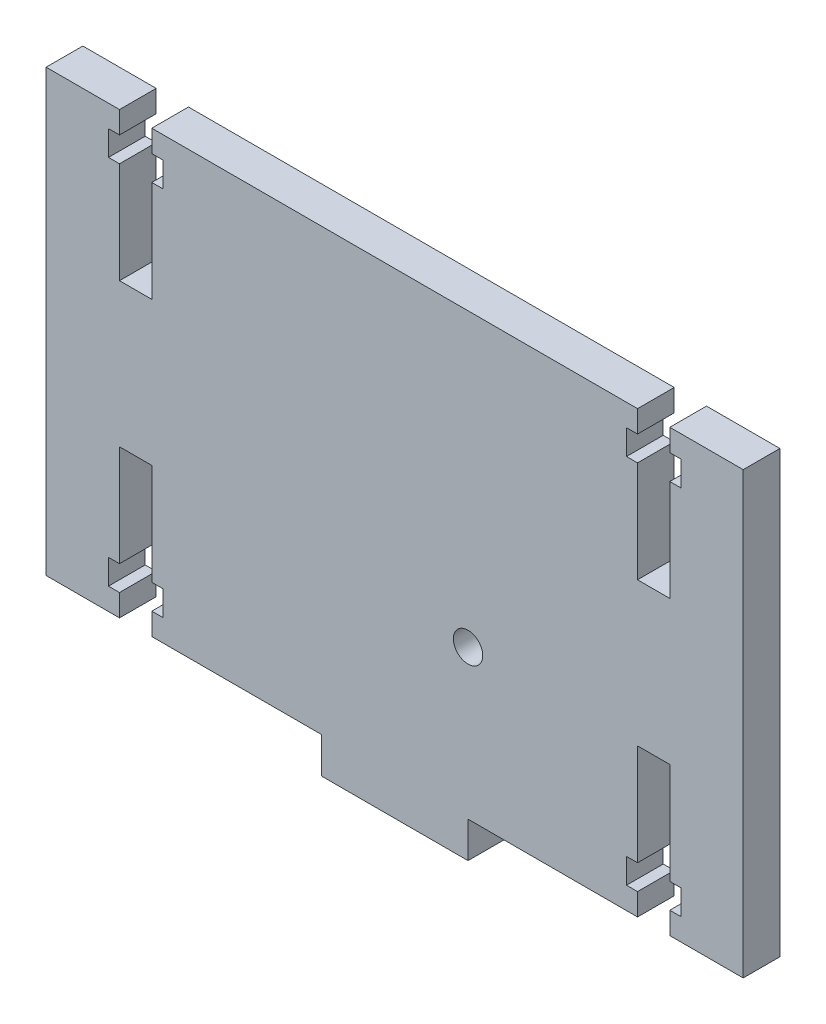
SolidWorks part; units mm, degrees
ref_plane "Front Plane" through (0, 0, 0) normal (0, 0, 1) x (1, 0, 0)
ref_plane "Top Plane" through (0, 0, 0) normal (0, 1, 0) x (1, 0, 0)
ref_plane "Right Plane" through (0, 0, 0) normal (1, 0, 0) x (0, 0, -1)
sketch "Sketch1" plane through (0, 0, 0) normal (0, 0, 1) x (1, 0, 0)
  line L0 (10, -30) -> (47.5, -30)
  line L1 (-47.5, 30) -> (47.5, 30)
  line L2 (-47.5, 30) -> (-47.5, -30)
  line L3 (-47.5, -30) -> (-10, -30)
  line L4 (47.5, 30) -> (47.5, -30)
  line L6 (-10, -30) -> (-10, -34.9)
  line L7 (-10, -34.9) -> (10, -34.9)
  line L8 (10, -30) -> (10, -34.9)
  dimension "D1" = 95
  dimension "D2" = 60
  dimension "D3" = 30
  dimension "D4" = 47.5
  dimension "D5" = 4.9
  dimension "D6" = 20
  dimension "D7" = 37.5
extrude "Boss-Extrude1" add sketch "Sketch1" along normal blind 5
sketch "Sketch3" plane through (0, 0, 5) normal (0, 0, 1) x (1, 0, 0)
  line L0 (-35.3, -30) -> (-35.3, -15.1548) construction
  line L1 (-33.1, -27) -> (-33.1, -30)
  line L2 (-37.5, -23.6) -> (-37.5, -9.8)
  line L3 (-31.6, -23.6) -> (-33.1, -23.6)
  line L4 (-31.6, -27) -> (-31.6, -23.6)
  line L5 (-33.1, -27) -> (-31.6, -27)
  line L6 (-39, -23.6) -> (-37.5, -23.6)
  line L7 (-39, -27) -> (-39, -23.6)
  line L8 (-37.5, -27) -> (-39, -27)
  line L9 (-37.5, -30) -> (-33.1, -30)
  line L10 (-33.1, -9.8) -> (-33.1, -23.6)
  line L11 (-37.5, -9.8) -> (-33.1, -9.8)
  line L12 (-37.5, -30) -> (-37.5, -27)
  line L13 (-47.5, -30) -> (-10, -30) construction
  line L14 (-47.5, 30) -> (-47.5, -30) construction
  line L15 (0, 0) -> (0, -21.795) construction
  line L16 (0, 0) -> (26.8997, 0) construction
  line L17 (35.3, -30) -> (35.3, -15.1548) construction
  line L18 (37.5, -30) -> (37.5, -27)
  line L19 (37.5, -9.8) -> (33.1, -9.8)
  line L20 (33.1, -9.8) -> (33.1, -23.6)
  line L21 (37.5, -30) -> (33.1, -30)
  line L22 (37.5, -27) -> (39, -27)
  line L23 (39, -27) -> (39, -23.6)
  line L24 (39, -23.6) -> (37.5, -23.6)
  line L25 (33.1, -27) -> (31.6, -27)
  line L26 (31.6, -27) -> (31.6, -23.6)
  line L27 (31.6, -23.6) -> (33.1, -23.6)
  line L28 (37.5, -23.6) -> (37.5, -9.8)
  line L29 (33.1, -27) -> (33.1, -30)
  line L30 (35.3, 30) -> (35.3, 15.1548) construction
  line L31 (33.1, 27) -> (33.1, 30)
  line L32 (37.5, 23.6) -> (37.5, 9.8)
  line L33 (31.6, 23.6) -> (33.1, 23.6)
  line L34 (31.6, 27) -> (31.6, 23.6)
  line L35 (33.1, 27) -> (31.6, 27)
  line L36 (39, 23.6) -> (37.5, 23.6)
  line L37 (39, 27) -> (39, 23.6)
  line L38 (37.5, 27) -> (39, 27)
  line L39 (37.5, 30) -> (33.1, 30)
  line L40 (33.1, 9.8) -> (33.1, 23.6)
  line L41 (37.5, 9.8) -> (33.1, 9.8)
  line L42 (37.5, 30) -> (37.5, 27)
  line L43 (-35.3, 30) -> (-35.3, 15.1548) construction
  line L44 (-37.5, 30) -> (-37.5, 27)
  line L45 (-37.5, 9.8) -> (-33.1, 9.8)
  line L46 (-33.1, 9.8) -> (-33.1, 23.6)
  line L47 (-37.5, 30) -> (-33.1, 30)
  line L48 (-37.5, 27) -> (-39, 27)
  line L49 (-39, 27) -> (-39, 23.6)
  line L50 (-39, 23.6) -> (-37.5, 23.6)
  line L51 (-33.1, 27) -> (-31.6, 27)
  line L52 (-31.6, 27) -> (-31.6, 23.6)
  line L53 (-31.6, 23.6) -> (-33.1, 23.6)
  line L54 (-37.5, 23.6) -> (-37.5, 9.8)
  line L55 (-33.1, 27) -> (-33.1, 30)
  dimension "D1" = 13.8
  dimension "D2" = 3.4
  dimension "D3" = 3
  dimension "D4" = 2.2
  dimension "D5" = 4.4
  dimension "D6" = 1.5
  dimension "D7" = 1.5
  dimension "D8" = 10
extrude "Cut-Extrude1" cut sketch "Sketch3" against normal blind 5
sketch "Sketch4" plane through (0, 0, 5) normal (0, 0, 1) x (1, 0, 0)
  circle A0 centre (10, -9.7) radius 2
  dimension "D1" = 4
extrude "Cut-Extrude2" cut sketch "Sketch4" against normal blind 5
